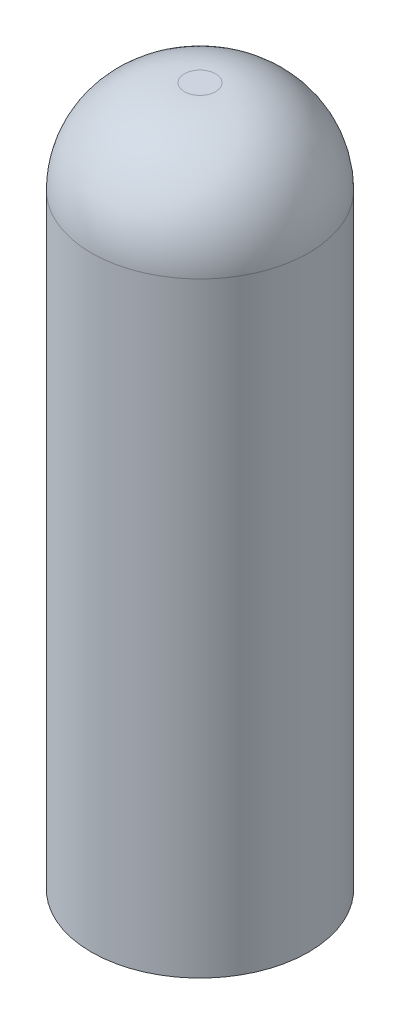
SolidWorks part; units mm, degrees
ref_plane "Front" through (0, 0, 0) normal (0, 0, 1) x (1, 0, 0)
ref_plane "Top" through (0, 0, 0) normal (0, 1, 0) x (1, 0, 0)
ref_plane "Right" through (0, 0, 0) normal (1, 0, 0) x (0, 0, -1)
sketch "Sketch1" plane through (0, 0, 0) normal (0, 1, 0) x (1, 0, 0)
  circle A0 centre (0, 0) radius 7
  dimension "D1" = 14
extrude "Boss-Extrude1" add sketch "Sketch1" along normal blind 45
fillet "Fillet1" radius 6 1 edges at (0, 45, 7)
sketch "Sketch2" plane through (0, 0, 0) normal (0, -1, 0) x (1, 0, 0)
  circle A0 centre (0, 0) radius 2.05
  dimension "D1" = 4.1
extrude "Cut-Extrude1" cut sketch "Sketch2" against normal blind 6
